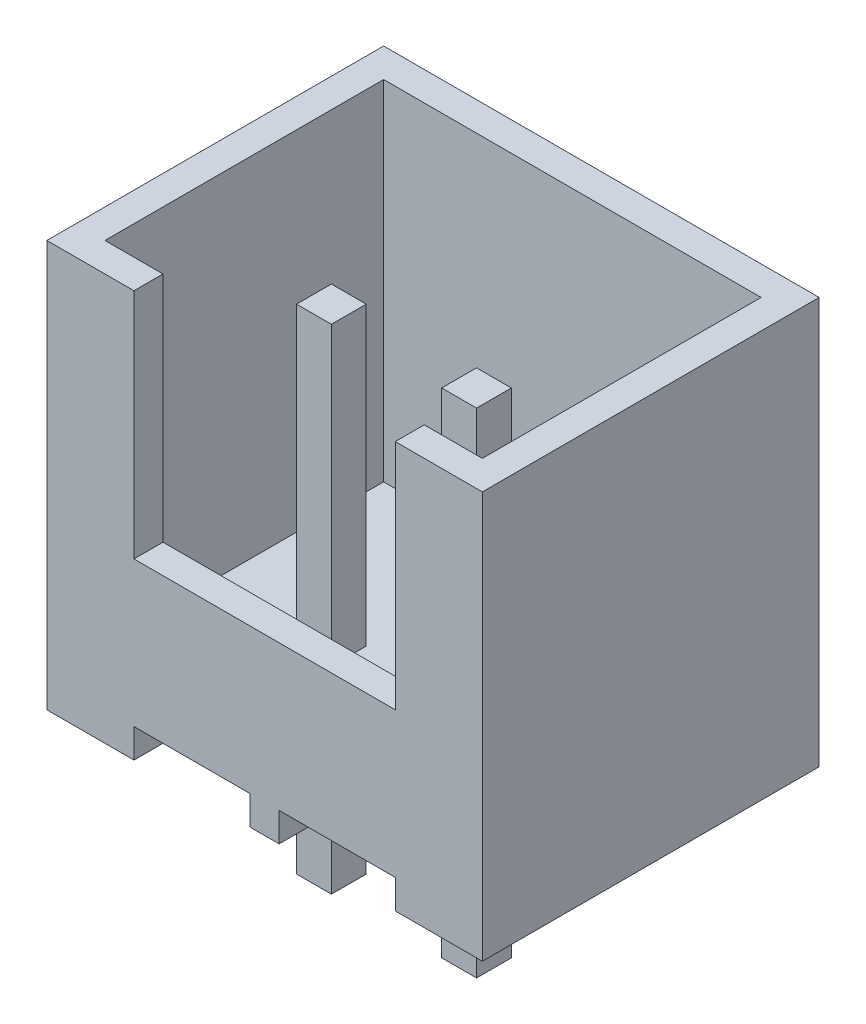
SolidWorks part; units mm, degrees
ref_plane "前视基准面" through (0, 0, 0) normal (0, 0, 1) x (1, 0, 0)
ref_plane "上视基准面" through (0, 0, 0) normal (0, 1, 0) x (1, 0, 0)
ref_plane "右视基准面" through (0, 0, 0) normal (1, 0, 0) x (0, 0, -1)
sketch "草图1" plane through (0, 0, 0) normal (0, 0, 1) x (1, 0, 0)
  line L0 (1.5, 0) -> (1.5, 0.5)
  line L1 (0, 0) -> (1.5, 0)
  line L2 (0, 0) -> (0, 7)
  line L3 (0, 7) -> (7.5, 7)
  line L4 (7.5, 0) -> (7.5, 7)
  line L5 (1.5, 0.5) -> (3.5, 0.5)
  line L6 (3.5, 0.5) -> (3.5, 0)
  line L7 (4, 0) -> (4, 0.5)
  line L8 (4, 0.5) -> (6, 0.5)
  line L9 (6, 0.5) -> (6, 0)
  line L10 (3.5, 0) -> (4, 0)
  line L11 (6, 0) -> (7.5, 0)
  line L12 (3.75, 4.6706) -> (3.75, 50004.6706) construction
  dimension "D1" = 7.5
  dimension "D2" = 7
  dimension "D3" = 2.5
  dimension "D4" = 0.5
  dimension "D5" = 0.5
extrude "凸台-拉伸1" add sketch "草图1" along normal blind 5.8
sketch "草图2" plane through (0, 7, 0) normal (0, 1, 0) x (1, 0, 0)
  line L0 (0, -5.8) -> (0, 0) construction
  line L1 (0.5, -0.5) -> (7, -0.5)
  line L2 (0.5, -0.5) -> (0.5, -5.3)
  line L3 (0.5, -5.3) -> (7, -5.3)
  line L4 (7, -0.5) -> (7, -5.3)
  line L5 (7.5, 0) -> (0, 0) construction
  line L6 (7.5, -5.8) -> (7.5, 0) construction
  line L7 (7.5, -5.8) -> (0, -5.8) construction
  dimension "D1" = 0.5
  dimension "D2" = 0.5
  dimension "D3" = 0.5
  dimension "D4" = 0.5
extrude "切除-拉伸1" cut sketch "草图2" against normal blind 6
sketch "草图3" plane through (0, 0, 0) normal (0, -1, 0) x (1, 0, 0)
  line L0 (1.5, 0) -> (3.5, 0) construction
  line L1 (2.2, 3.7) -> (2.8, 3.7)
  line L2 (2.2, 3.7) -> (2.2, 3.1)
  line L3 (2.2, 3.1) -> (2.8, 3.1)
  line L4 (2.8, 3.7) -> (2.8, 3.1)
  line L5 (2.5, 4.7075) -> (2.5, 50004.7075) construction
  line L6 (1.5, 5.8) -> (1.5, 0) construction
  line L7 (3.5, 5.8) -> (3.5, 0) construction
  line L8 (3.75, 2.7254) -> (3.75, 50002.7254) construction
  line L9 (0, 5.8) -> (0, 0) construction
  line L10 (7.5, 5.8) -> (7.5, 0) construction
  line L11 (4.7, 3.7) -> (4.7, 3.1)
  line L12 (5.3, 3.1) -> (4.7, 3.1)
  line L13 (5.3, 3.7) -> (5.3, 3.1)
  line L14 (5.3, 3.7) -> (4.7, 3.7)
  dimension "D1" = 0.6
  dimension "D2" = 3.1
  dimension "D3" = 2.5
extrude "凸台-拉伸2" add sketch "草图3" against normal blind 6.1 and the other way blind 2.4
sketch "草图5" plane through (0, 0, 5.8) normal (0, 0, 1) x (1, 0, 0)
  line L0 (0, 7) -> (0, 0) construction
  line L2 (1.5, 7) -> (1.5, 3)
  line L3 (7.5, 7) -> (0, 7) construction
  line L4 (1.5, 3) -> (6, 3)
  line L5 (6, 3) -> (6, 7)
  line L6 (1.5, 7) -> (6, 7)
  line L7 (7.5, 0) -> (7.5, 7) construction
  dimension "D1" = 1.5
  dimension "D2" = 1.5
  dimension "D3" = 4
extrude "切除-拉伸2" cut sketch "草图5" against normal blind 1
